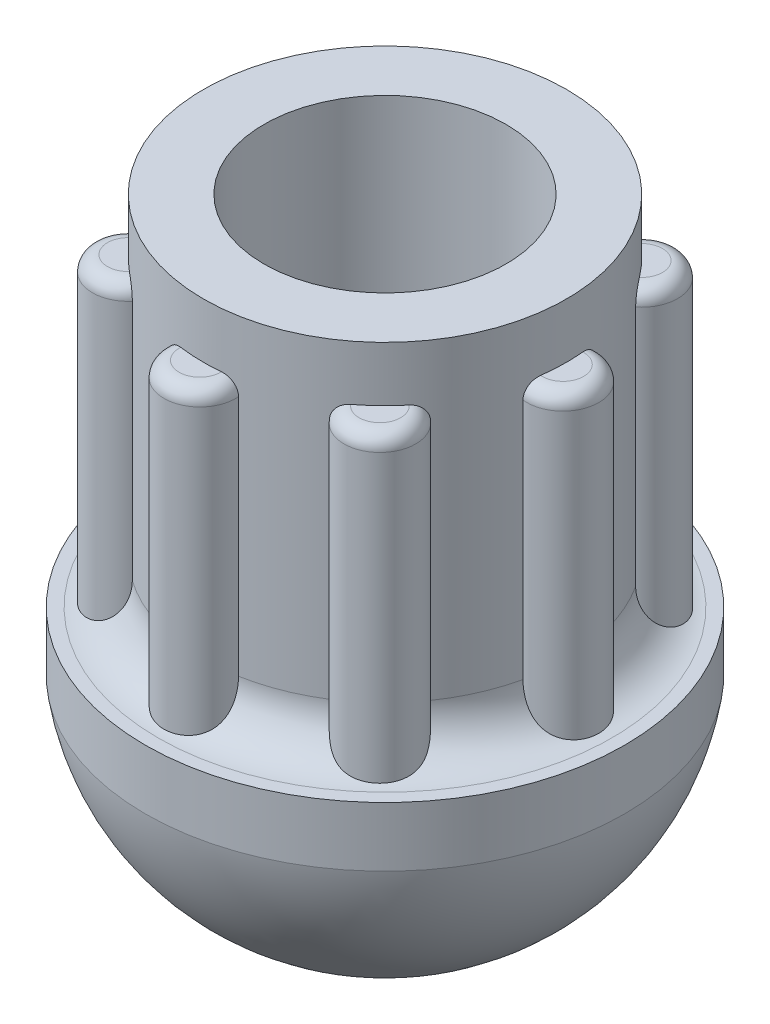
SolidWorks part; units mm, degrees
ref_plane "Front Plane" through (0, 0, 0) normal (0, 0, 1) x (1, 0, 0)
ref_plane "Top Plane" through (0, 0, 0) normal (0, 1, 0) x (1, 0, 0)
ref_plane "Right Plane" through (0, 0, 0) normal (1, 0, 0) x (0, 0, -1)
sketch "Sketch1" plane through (0, 0, 0) normal (0, 0, 1) x (1, 0, 0)
  line L0 (0, 0) -> (0, 8.8247)
  line L1 (0, 8.8247) -> (2.5, 8.8247)
  line L2 (4, 10.3247) -> (4, 20.6375)
  line L3 (4, 20.6375) -> (6, 20.6375)
  line L4 (6, 20.6375) -> (6, 10.3247)
  line L5 (7.5, 8.8247) -> (7.9182, 8.8247)
  line L6 (7.9182, 8.8247) -> (7.9182, 6.8589)
  arc A0 (0, 0) -> (7.9182, 6.8589) centre (0, 8) ccw
  arc A1 (2.5, 8.8247) -> (4, 10.3247) centre (2.5, 10.3247) ccw
  arc A2 (6, 10.3247) -> (7.5, 8.8247) centre (7.5, 10.3247) ccw
  point P4 (5, 20.6375)
  point P14 (4, 8.8247)
  dimension "D1" = 16
  dimension "D5" = 1.5
  dimension "D2" = 4
  dimension "D3" = 2
  dimension "D4" = 20.6375
revolve "Revolve1" add sketch "Sketch1" angle 360 about L0
sketch "Sketch2" plane through (0, 8.8247, 0) normal (0, 1, 0) x (1, 0, 0)
  circle A0 centre (0.1189, 5.9988) radius 1.1867
  circle A1 centre (0, 0) radius 6 construction
  circle A2 centre (4.3259, 4.1577) radius 1.1867
  circle A3 centre (5.9988, -0.1189) radius 1.1867
  circle A4 centre (4.1577, -4.3259) radius 1.1867
  circle A5 centre (-0.1189, -5.9988) radius 1.1867
  circle A6 centre (-4.3259, -4.1577) radius 1.1867
  circle A7 centre (-5.9988, 0.1189) radius 1.1867
  circle A8 centre (-4.1577, 4.3259) radius 1.1867
  point P21 (0, 0)
  dimension "D1" = 8
extrude "Boss-Extrude1" add sketch "Sketch2" along normal blind 10
fillet "Fillet1" radius 0.5 8 edges at (-5.1815, 18.8247, 4.98) (-7.1853, 18.8247, -0.1425) (-4.98, 18.8247, -5.1815) (0.1425, 18.8247, -7.1853) (-0.1425, 18.8247, 7.1853) (4.98, 18.8247, 5.1815) (5.1815, 18.8247, -4.98) (7.1853, 18.8247, 0.1425)
